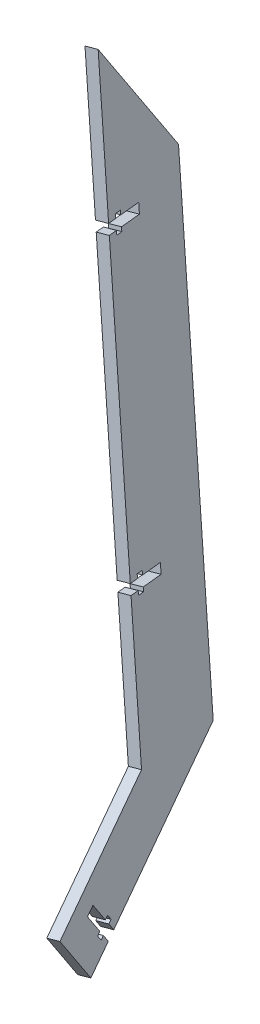
SolidWorks part; units mm, degrees
ref_plane "Front Plane" through (0, 0, 0) normal (0, 0, 1) x (1, 0, 0)
ref_plane "Top Plane" through (0, 0, 0) normal (0, 1, 0) x (1, 0, 0)
ref_plane "Right Plane" through (0, 0, 0) normal (1, 0, 0) x (0, 0, -1)
ref_plane "Plane1" through (-68.394, -9.004, 13.6994) normal (0.9725, 0.128, -0.1948) x (0.2331, -0.5341, 0.8126)
sketch "Sketch1" plane through (-68.394, -9.004, 13.6994) normal (0.9725, 0.128, -0.1948) x (0.2331, -0.5341, 0.8126)
  line L0 (290.7345, 269.4716) -> (290.7345, 334.4423)
  line L1 (290.7345, 269.4716) -> (446.7605, 469.1757)
  line L2 (290.7345, 334.4423) -> (415.5319, 494.1757)
  line L4 (290.7345, 267.9716) -> (290.7345, 514.1757) construction
  line L5 (198.0169, 267.9716) -> (1170.4723, 267.9716) construction
  line L6 (937.3831, 267.9716) -> (-35.0723, 267.9716) construction
  line L7 (446.7605, 410.8725) -> (446.7605, 469.1757) construction
  line L11 (509.2605, 486.6757) -> (509.2605, 466.6757) construction
  line L12 (415.5319, 494.1757) -> (509.2605, 494.1757)
  line L14 (446.7605, 469.1757) -> (509.2605, 469.1757)
  line L15 (509.2605, 494.1757) -> (509.2605, 469.1757)
  line L17 (449.2605, 486.6757) -> (449.2605, 466.6757) construction
  dimension "D1" = 201.2042
  dimension "D2" = 25
  dimension "D3" = 2.5
  dimension "D4" = 38
  dimension "D5" = 1.5
  dimension "D6" = 40
extrude "Boss-Extrude1" add sketch "Sketch1" along normal blind 5
sketch "Sketch3" plane through (-63.5317, -8.3639, 12.7255) normal (0.9725, 0.128, -0.1948) x (-0.1931, -0.0254, -0.9808)
  line L0 (-103.2082, -577.7785) -> (-102.9192, -573.5885)
  line L1 (-103.2082, -577.7785) -> (-99.2177, -578.0538)
  line L2 (-102.9192, -573.5885) -> (-98.9287, -573.8637)
  line L3 (-99.3347, -579.7498) -> (-99.2177, -578.0538)
  line L4 (-99.3347, -579.7498) -> (-96.5414, -579.9425)
  line L5 (-98.8117, -572.1678) -> (-96.0183, -572.3605)
  line L6 (-96.5414, -579.9425) -> (-96.4244, -578.2465)
  line L7 (-96.4244, -578.2465) -> (-86.4481, -578.9347)
  line L8 (-96.1353, -574.0565) -> (-86.159, -574.7447)
  line L9 (-86.4481, -578.9347) -> (-86.159, -574.7447)
  line L10 (-96.1353, -574.0565) -> (-96.0183, -572.3605)
  line L11 (-98.9287, -573.8637) -> (-98.8117, -572.1678)
  line L12 (-94.4873, -451.3648) -> (-94.1982, -447.1748)
  line L13 (-94.4873, -451.3648) -> (-90.4968, -451.6401)
  line L14 (-89.9823, -386.063) -> (-107.4242, -638.8903) construction
  line L15 (-94.1982, -447.1748) -> (-90.2077, -447.4501)
  line L16 (-90.6138, -453.3361) -> (-90.4968, -451.6401)
  line L17 (-90.6138, -453.3361) -> (-87.8204, -453.5288)
  line L18 (-90.0907, -445.7541) -> (-87.2974, -445.9468)
  line L19 (-87.8204, -453.5288) -> (-87.7034, -451.8328)
  line L20 (-87.7034, -451.8328) -> (-77.7271, -452.5211)
  line L21 (-87.4144, -447.6428) -> (-77.4381, -448.331)
  line L22 (-77.7271, -452.5211) -> (-77.4381, -448.331)
  line L23 (-87.4144, -447.6428) -> (-87.2974, -445.9468)
  line L24 (-90.2077, -447.4501) -> (-90.0907, -445.7541)
  line L25 (-98.7032, -512.4766) -> (-107.4242, -638.8903) construction
  line L26 (-89.9823, -386.063) -> (-98.7032, -512.4766) construction
  line L27 (-77.5826, -450.4261) -> (-94.3428, -449.2698) construction
  line L28 (-86.3036, -576.8397) -> (-103.0637, -575.6835) construction
  line L29 (-130.6718, -684.7771) -> (-134.1515, -687.129)
  line L30 (-130.6718, -684.7771) -> (-132.9116, -681.4631)
  line L31 (-134.1515, -687.129) -> (-136.3914, -683.8149)
  line L32 (-131.5032, -680.5111) -> (-132.9116, -681.4631)
  line L33 (-131.5032, -680.5111) -> (-133.0711, -678.1913)
  line L34 (-137.7999, -684.7669) -> (-139.3678, -682.447)
  line L35 (-133.0711, -678.1913) -> (-134.4796, -679.1432)
  line L36 (-134.4796, -679.1432) -> (-140.0792, -670.8581)
  line L37 (-137.9593, -681.4951) -> (-143.559, -673.21)
  line L38 (-140.0792, -670.8581) -> (-143.559, -673.21)
  line L39 (-137.9593, -681.4951) -> (-139.3678, -682.447)
  line L40 (-136.3914, -683.8149) -> (-137.7999, -684.7669)
  line L41 (-141.8191, -672.034) -> (-132.4117, -685.9531) construction
  line L42 (-159.2063, -673.8883) -> (-133.6154, -656.5921) construction
  line L43 (-76.053, -741.76) -> (-103.9371, -700.5034) construction
  line L44 (-145.2071, -694.6011) -> (-67.5517, -642.1162) construction
  line L45 (-132.4117, -685.9531) -> (-146.4109, -665.2402) construction
  line L46 (-107.4242, -638.8903) -> (-159.2063, -673.8883) construction
  dimension "D1" = 4.2
  dimension "D2" = 1.7
  dimension "D3" = 1.7
  dimension "D4" = 2.8
  dimension "D5" = 10
  dimension "D6" = 4
  dimension "D7" = 4.2
  dimension "D8" = 1.7
  dimension "D9" = 1.7
  dimension "D10" = 2.8
  dimension "D11" = 10
  dimension "D12" = 4
  dimension "D13" = 4.2
  dimension "D14" = 1.7
  dimension "D15" = 1.7
  dimension "D16" = 2.8
  dimension "D17" = 10
  dimension "D18" = 4
extrude "Cut-Extrude2" cut sketch "Sketch3" against normal through all
